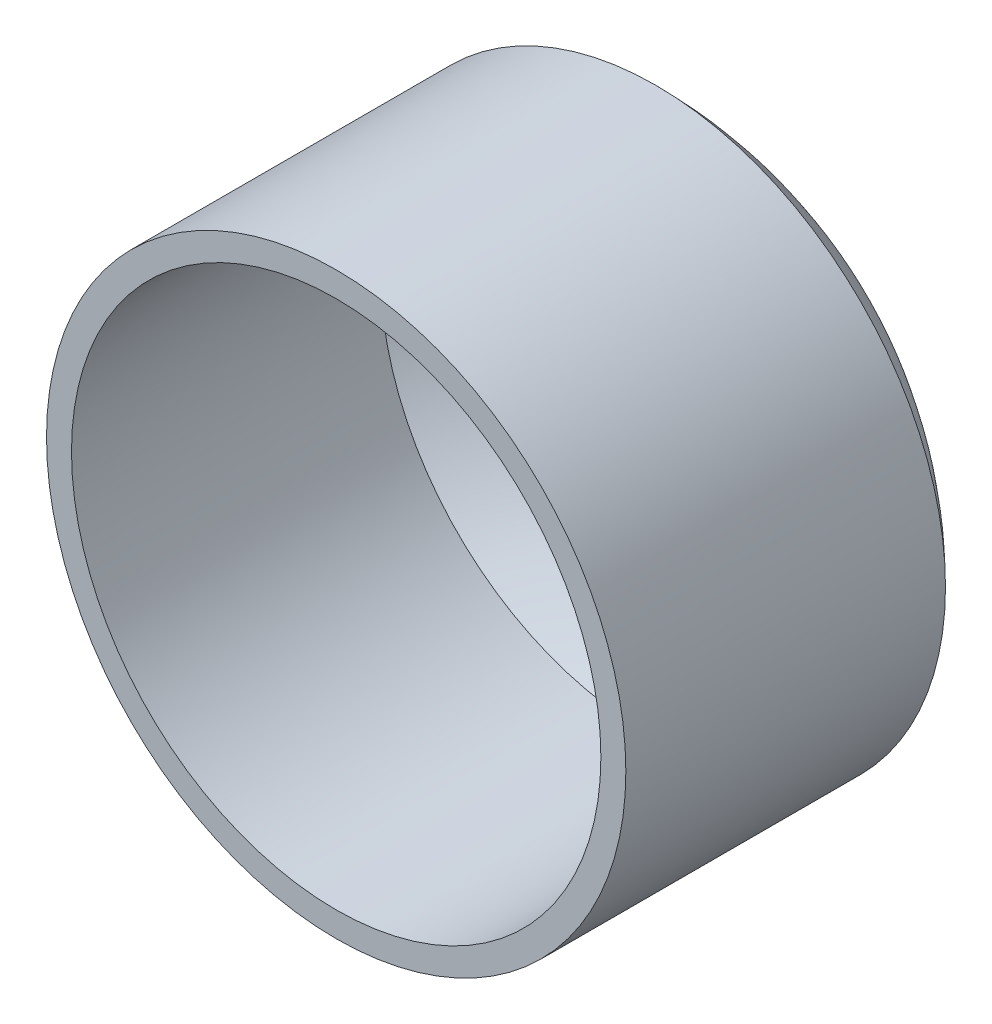
SolidWorks part; units mm, degrees
material "PVC Rigid"
ref_plane "Front Plane" through (0, 0, 0) normal (0, 0, 1) x (1, 0, 0)
ref_plane "Top Plane" through (0, 0, 0) normal (0, 1, 0) x (1, 0, 0)
ref_plane "Right Plane" through (0, 0, 0) normal (1, 0, 0) x (0, 0, -1)
sketch "Sketch1" plane through (0, 0, 0) normal (0, 0, 1) x (1, 0, 0)
  circle A1 centre (0, 0) radius 92.075
  dimension "D3" = 184.15
extrude "Boss-Extrude1" add sketch "Sketch1" along normal blind 101.6
sketch "Sketch2" plane through (0, 0, 0) normal (1, 0, 0) x (0, 0, -1)
  line L1 (0, 0) -> (38.1, 0)
  line L2 (0, -92.075) -> (0, 92.075) construction
  line L3 (0, 0) -> (0, 92.075)
  arc A0 (0, 92.075) -> (38.1, 0) centre (-92.2073, 0) cw
  dimension "D1" = 38.1
revolve "Revolve1" add sketch "Sketch2" angle 360 about L1
shell "Shell1" thickness 7.9375
